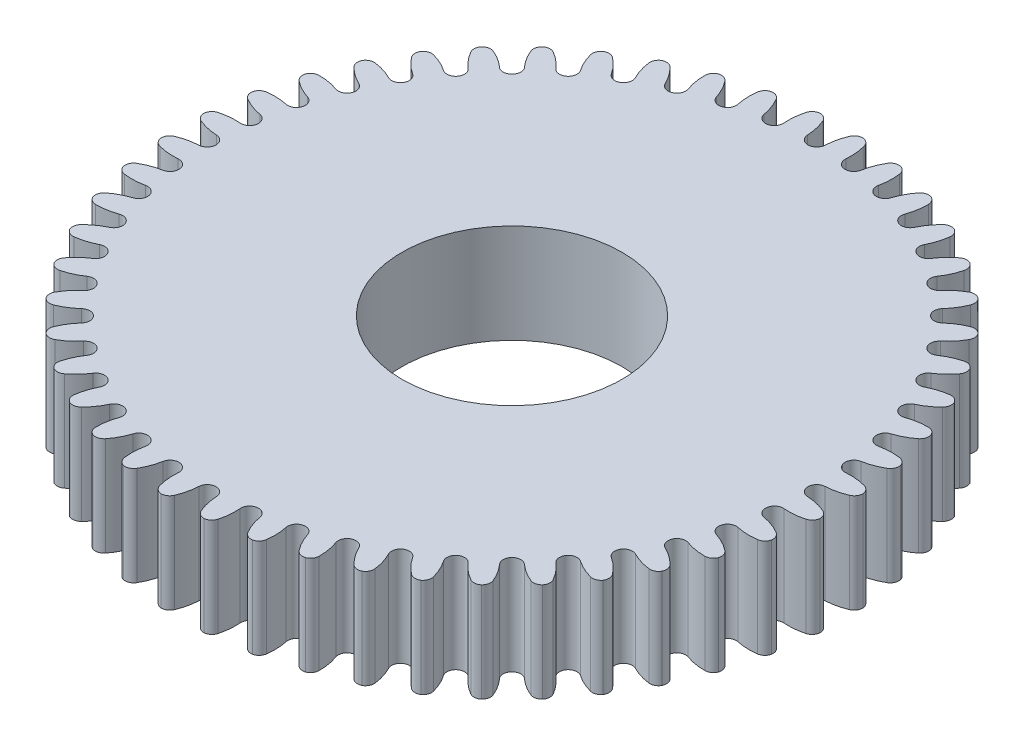
SolidWorks part; units mm, degrees
ref_plane "Front Plane" through (0, 0, 0) normal (0, 0, 1) x (1, 0, 0)
ref_plane "Top Plane" through (0, 0, 0) normal (0, 1, 0) x (1, 0, 0)
ref_plane "Right Plane" through (0, 0, 0) normal (1, 0, 0) x (0, 0, -1)
sketch "Sketch1" plane through (0, 0, 0) normal (0, 1, 0) x (1, 0, 0)
  circle A0 centre (0, 0) radius 30
  dimension "D1" = 60
extrude "Boss-Extrude1" add sketch "Sketch1" along normal blind 9
sketch "Sketch3" plane through (0, 0, 0) normal (0, -1, 0) x (1, 0, 0)
  line L0 (0, -27.6851) -> (0, -60.2569) construction
  arc A0 (0.7992, -27.6484) -> (-0.7992, -27.6484) centre (0, -27.6851) ccw
  arc A1 (0.7992, -27.6484) -> (1.2101, -29.4488) centre (5.9937, -27.4099) ccw
  circle A2 centre (1.946, -29.1351) radius 0.8
  circle A3 centre (0, 0) radius 30 construction
  circle A4 centre (-1.946, -29.1351) radius 0.8
  arc A5 (-0.7992, -27.6484) -> (-1.2101, -29.4488) centre (-5.9937, -27.4099) cw
  dimension "D1" = 1.6
  dimension "D2" = 10.4
  dimension "D3" = 1.45
  dimension "D4" = 1.6
  dimension "D5" = 3.892
extrude "Cut-Extrude1" cut sketch "Sketch3" against normal blind 9
pattern_circular "CirPattern1" count 48 over 360 about axis through (0, 0, 0) along (0, 1, 0) of "Cut-Extrude1"
sketch "Sketch4" plane through (0, 0, 0) normal (0, -1, 0) x (1, 0, 0)
  circle A0 centre (0, 0) radius 10
  dimension "D1" = 20
extrude "Cut-Extrude3" cut sketch "Sketch4" against normal blind 9
